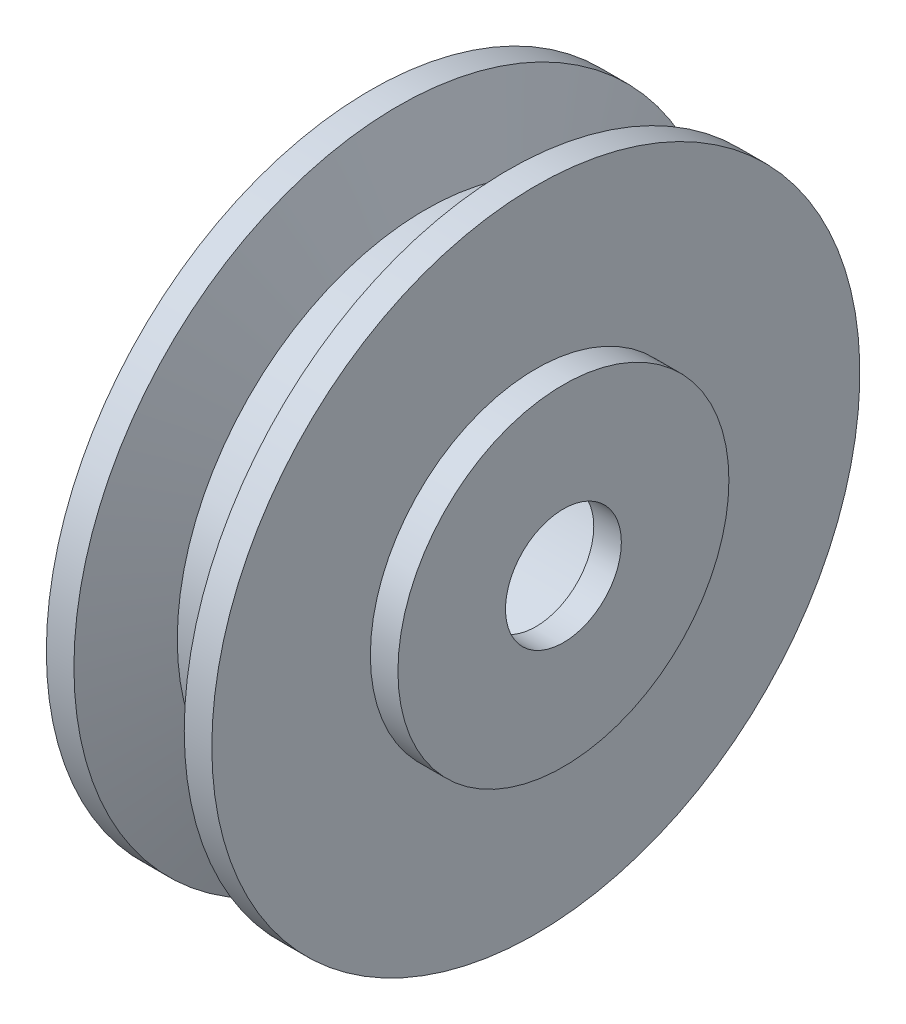
SolidWorks part; units mm, degrees
other "Markup1"
sketch "Sketch6" plane through (3.525, 10.4424, 10.4424) normal (0.3992, 0.122, 0.9087) x (0.9073, 0.0902, -0.4107)
ref_plane "Front Plane" through (0, 0, 0) normal (0, 0, 1) x (1, 0, 0)
ref_plane "Top Plane" through (0, 0, 0) normal (0, 1, 0) x (1, 0, 0)
ref_plane "Right Plane" through (0, 0, 0) normal (1, 0, 0) x (0, 0, -1)
sketch "Sketch1" plane through (0, 0, 0) normal (0, 0, 1) x (1, 0, 0)
  line L0 (0, 0) -> (19.9602, 0) construction
  line L1 (0, 0) -> (0, 9)
  line L2 (0, 9) -> (1, 9)
  line L3 (1, 9) -> (2, 11.7475)
  line L4 (2, 11.7475) -> (3, 11.7475)
  line L5 (3, 11.7475) -> (3, 0)
  line L6 (3, 0) -> (0, 0)
  dimension "D1" = 1
  dimension "D2" = 9
  dimension "D3" = 1
  dimension "D4" = 110
  dimension "D5" = 1
revolve "Revolve1" add sketch "Sketch1" angle 360 about L0
mirror "Mirror1" about plane through (0, 0, 0) normal (1, 0, 0) of "Revolve1"
sketch "Sketch3" plane through (3, 0, 0) normal (1, 0, 0) x (0, 0, -1)
  circle A0 centre (0, 0) radius 5
extrude "Cut-Extrude1" cut sketch "Sketch3" against normal blind 87
sketch "Sketch5" plane through (3, 0, 0) normal (1, 0, 0) x (0, 0, -1)
  circle A0 centre (0, 0) radius 6
  circle A1 centre (0, 0) radius 2.1
extrude "Boss-Extrude2" add sketch "Sketch5" along normal blind 1
sketch "Sketch7" plane through (-3, 0, 0) normal (-1, 0, 0) x (0, 0, 1)
  circle A0 centre (0, 0) radius 6
  circle A1 centre (0, 0) radius 2.1
extrude "Boss-Extrude3" add sketch "Sketch7" along normal blind 1 separate body
